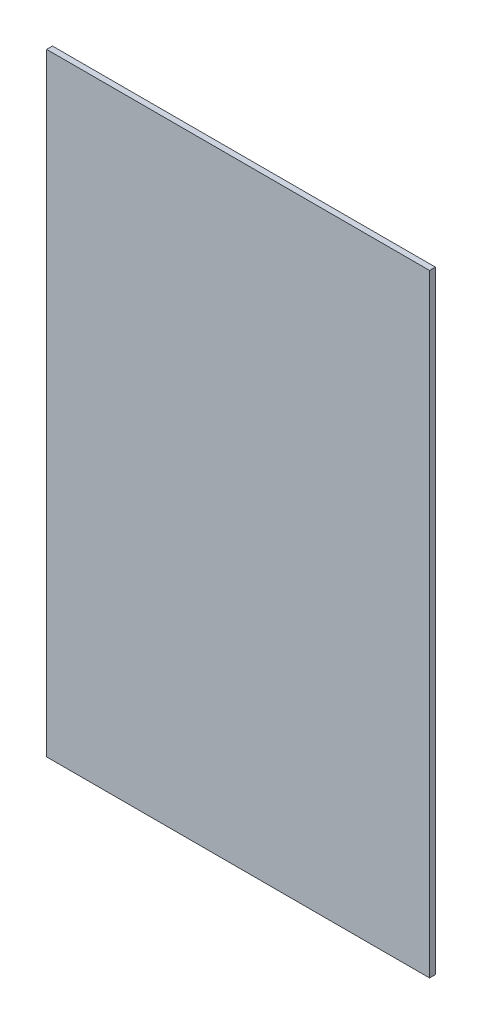
SolidWorks part; units mm, degrees
material "Plain Carbon Steel"
ref_plane "Front Plane" through (0, 0, 0) normal (0, 0, 1) x (1, 0, 0)
ref_plane "Top Plane" through (0, 0, 0) normal (0, 1, 0) x (1, 0, 0)
ref_plane "Right Plane" through (0, 0, 0) normal (1, 0, 0) x (0, 0, -1)
sketch "Sketch1" plane through (0, 0, 0) normal (0, 0, 1) x (1, 0, 0)
  line L1 (0, 0) -> (50, 0)
  line L2 (0, 0) -> (0, 80)
  line L3 (0, 80) -> (50, 80)
  line L4 (50, 0) -> (50, 80)
  dimension "D1" = 50
  dimension "D2" = 80
extrude "Boss-Extrude1" add sketch "Sketch1" along normal blind 0.76 contours L2 L3 L4 L1
ref_plane "Plane1" through (25, 0, 0) normal (1, 0, 0) x (0, 0, -1)
